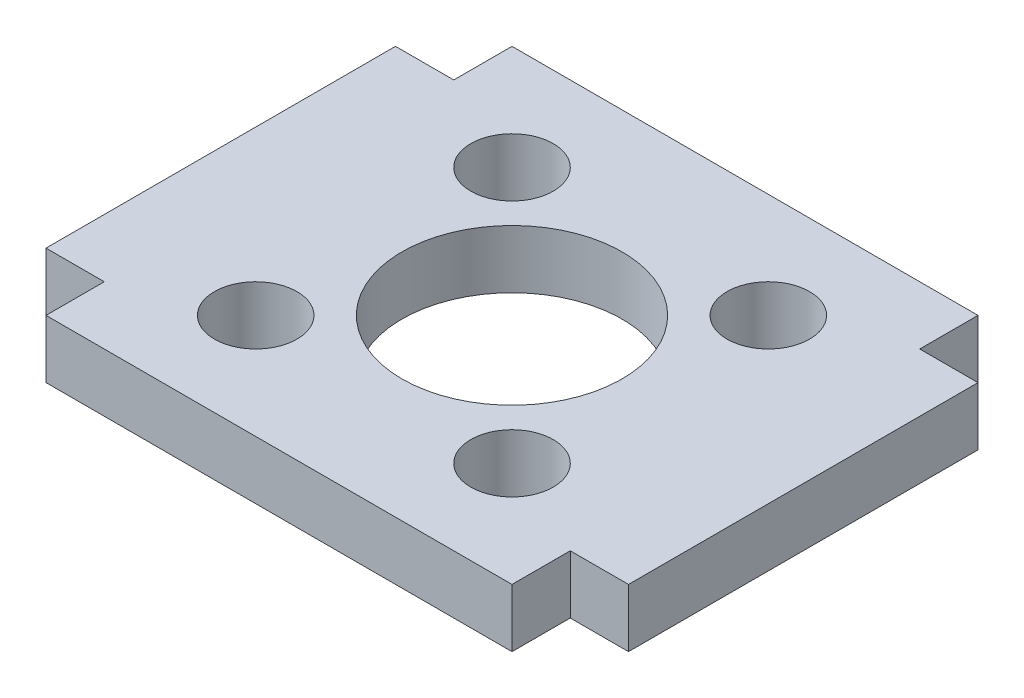
SolidWorks part; units mm, degrees
material "6061-T6 (SS)"
ref_plane "Front Plane" through (0, 0, 0) normal (0, 0, 1) x (1, 0, 0)
ref_plane "Top Plane" through (0, 0, 0) normal (0, 1, 0) x (1, 0, 0)
ref_plane "Right Plane" through (0, 0, 0) normal (1, 0, 0) x (0, 0, -1)
sketch "Sketch1" plane through (0, 0, 0) normal (0, 1, 0) x (1, 0, 0)
  line L0 (-12.7, 9.525) -> (-15.875, 9.525)
  line L1 (12.7, -12.7) -> (-12.7, -12.7)
  line L2 (12.7, -12.7) -> (12.7, -9.525)
  line L3 (12.7, 12.7) -> (-12.7, 12.7)
  line L4 (-12.7, -12.7) -> (-12.7, -9.525)
  line L5 (12.7, -12.7) -> (-12.7, 12.7) construction
  line L6 (12.7, 12.7) -> (-12.7, -12.7) construction
  line L7 (-15.875, 9.525) -> (-15.875, -9.525)
  line L8 (-15.875, -9.525) -> (-12.7, -9.525)
  line L9 (12.7, 9.525) -> (15.875, 9.525)
  line L10 (15.875, 9.525) -> (15.875, -9.525)
  line L11 (15.875, -9.525) -> (12.7, -9.525)
  line L12 (12.7, 9.525) -> (12.7, 12.7)
  line L13 (-12.7, 9.525) -> (-12.7, 12.7)
  point P0 (0, 0)
  dimension "D1" = 19.05
  dimension "D2" = 3.175
  dimension "D3" = 25.4
  dimension "D4" = 25.4
  dimension "D5" = 3.175
extrude "Boss-Extrude1" add sketch "Sketch1" along normal blind 3.175
sketch "Sketch2" plane through (0, 3.175, 0) normal (0, 1, 0) x (1, 0, 0)
  circle A0 centre (0, 0) radius 6
  dimension "D1" = 12
extrude "Cut-Extrude1" cut sketch "Sketch2" against normal through all
hole_wizard "#8 Clearance Hole1" positions "Sketch3" profile "Sketch4" hole size "#8" standard "ANSI Inch" end condition through all
sketch "Sketch3" plane through (0, 3.175, 0) normal (0, 1, 0) x (1, 0, 0)
  line L0 (-6.985, -6.985) -> (6.985, 6.985) construction
  line L2 (-6.985, 6.985) -> (6.985, -6.985) construction
  circle A0 centre (0, 0) radius 6 construction
  point P0 (-6.985, 6.985)
  point P2 (6.985, 6.985)
  point P4 (6.985, -6.985)
  point P6 (-6.985, -6.985)
  point P18 (0, 0)
  dimension "D1" = 13.97
sketch "Sketch4" plane through (-6.985, 3.175, -6.985) normal (1, 0, 0) x (0, 0, 1)
  line L0 (0, 0) -> (0, 3.175)
  line L1 (0, 3.175) -> (2.2479, 3.175)
  line L2 (2.2479, 3.175) -> (2.2479, 0)
  line L5 (2.2479, 0) -> (0, 0)
  line L11 (0, -6.35) -> (0, 107.95) construction
  dimension "Thru Hole Dia." = 4.4958
  dimension "Thru Hole Depth" = 3.175
